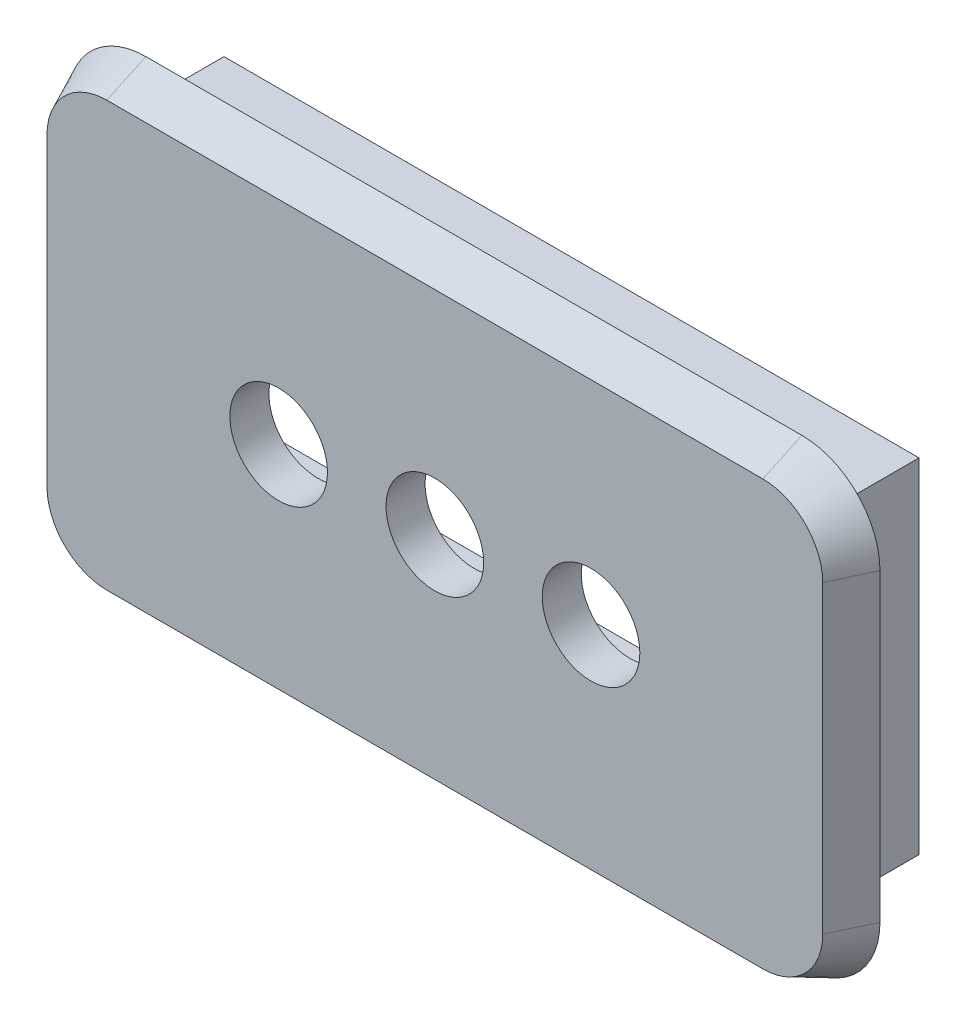
SolidWorks part; units mm, degrees
ref_plane "前视基准面" through (0, 0, 0) normal (0, 0, 1) x (1, 0, 0)
ref_plane "上视基准面" through (0, 0, 0) normal (0, 1, 0) x (1, 0, 0)
ref_plane "右视基准面" through (0, 0, 0) normal (1, 0, 0) x (0, 0, -1)
other "Configuration Table"
sketch "草图1" plane through (0, 0, 0) normal (0, 0, 1) x (1, 0, 0)
  line L4 (-7.465, 28.9) -> (-7.465, 22.1)
  line L5 (-7.465, 22.1) -> (8.335, 22.1)
  line L6 (8.335, 22.1) -> (8.335, 28.9)
  line L7 (8.335, 28.9) -> (-7.465, 28.9)
  line L12 (-8.465, 29.9) -> (-8.465, 21.1)
  line L13 (-8.465, 21.1) -> (9.335, 21.1)
  line L14 (9.335, 21.1) -> (9.335, 29.9)
  line L15 (9.335, 29.9) -> (-8.465, 29.9)
  dimension "D1" = 8.8
  dimension "D2" = 17.8
extrude "凸台-拉伸1" add sketch "草图1" against normal blind 2.5
sketch "草图2" plane through (0, 0, 0) normal (0, 0, 1) x (1, 0, 0)
  line L8 (10.835, 19.6) -> (10.835, 31.4)
  line L9 (-9.965, 19.6) -> (10.835, 19.6)
  line L10 (-9.965, 31.4) -> (-9.965, 19.6)
  line L11 (10.835, 31.4) -> (-9.965, 31.4)
  line L12 (10.835, 21.6) -> (10.835, 29.4)
  line L13 (-7.965, 19.6) -> (8.835, 19.6)
  line L14 (-9.965, 29.4) -> (-9.965, 21.6)
  line L15 (8.835, 31.4) -> (-7.965, 31.4)
  arc A0 (10.835, 29.4) -> (8.835, 31.4) centre (8.835, 29.4) ccw
  arc A1 (10.835, 21.6) -> (8.835, 19.6) centre (8.835, 21.6) cw
  arc A2 (-7.965, 19.6) -> (-9.965, 21.6) centre (-7.965, 21.6) cw
  arc A3 (-9.965, 29.4) -> (-7.965, 31.4) centre (-7.965, 29.4) cw
  dimension "D2" = 2
  dimension "D1" = 1.5
extrude "凸台-拉伸2" add sketch "草图2" along normal blind 1 draft 25
sketch "草图3" plane through (0, 0, 1) normal (0, 0, 1) x (1, 0, 0)
  line L0 (8.835, 30.9337) -> (-7.965, 30.9337) construction
  line L1 (-9.4987, 29.4) -> (-9.4987, 21.6) construction
  circle A0 centre (0.435, 25.5) radius 1.25
  circle A1 centre (-3.565, 25.5) radius 1.25
  circle A2 centre (4.435, 25.5) radius 1.25
  point P4 (0.435, 30.9337)
  point P7 (-9.4987, 25.5)
  dimension "D1" = 2.5
  dimension "D2" = 4
  dimension "D3" = 4
extrude "切除-拉伸1" cut sketch "草图3" against normal up to next
